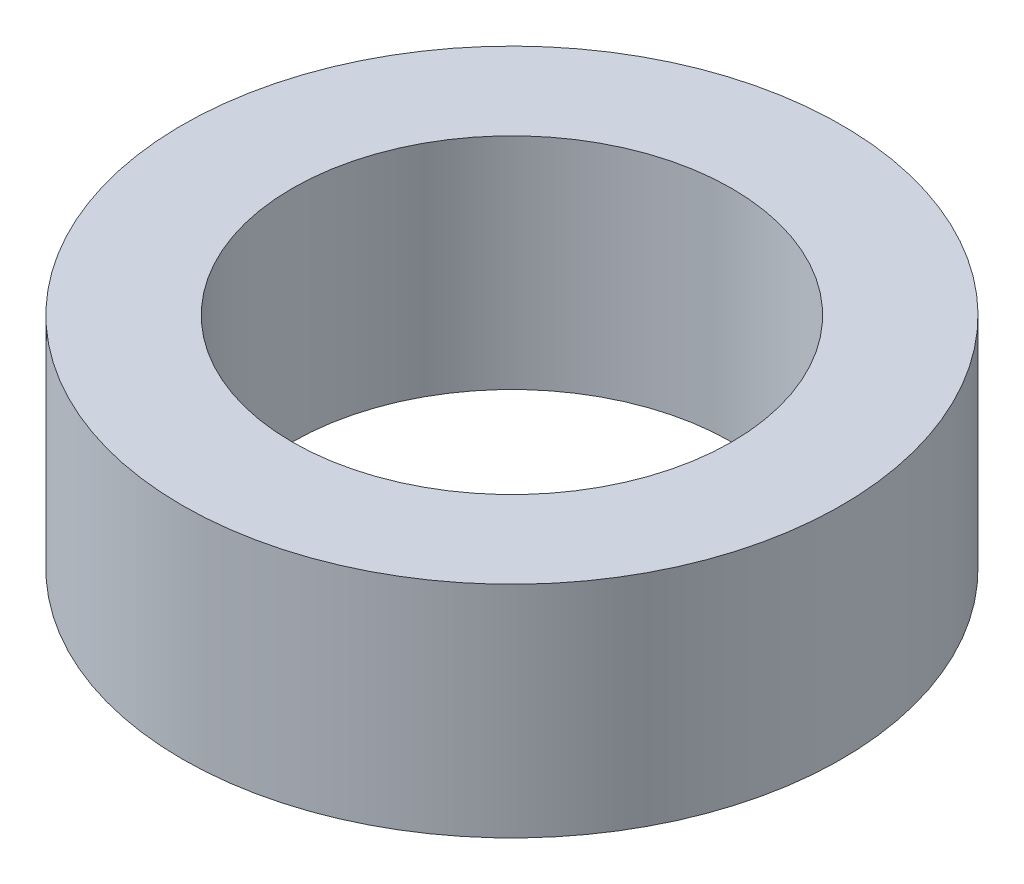
SolidWorks part; units mm, degrees
ref_plane "Front Plane" through (0, 0, 0) normal (0, 0, 1) x (1, 0, 0)
ref_plane "Top Plane" through (0, 0, 0) normal (0, 1, 0) x (1, 0, 0)
ref_plane "Right Plane" through (0, 0, 0) normal (1, 0, 0) x (0, 0, -1)
sketch "Sketch1" plane through (0, 0, 0) normal (0, 1, 0) x (1, 0, 0)
  circle A0 centre (0, 0) radius 12.7
  circle A1 centre (0, 0) radius 19.05
  dimension "D1" = 25.4
  dimension "D2" = 6.35
extrude "Boss-Extrude1" add sketch "Sketch1" along normal blind 12.7
